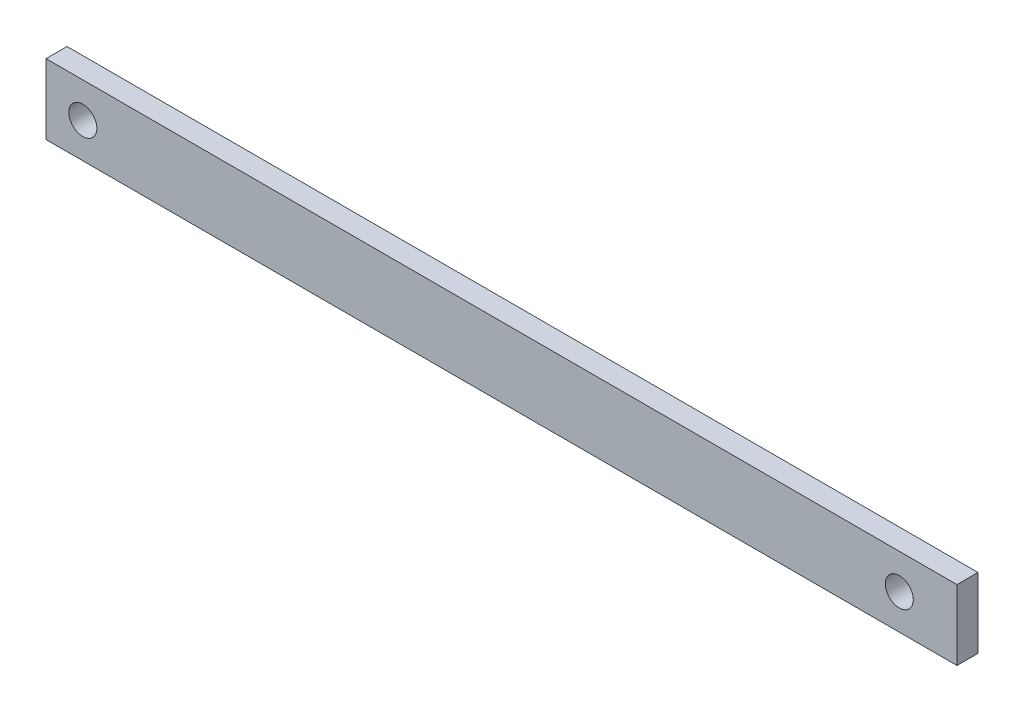
SolidWorks part; units mm, degrees
ref_plane "Front Plane" through (0, 0, 0) normal (0, 0, 1) x (1, 0, 0)
ref_plane "Top Plane" through (0, 0, 0) normal (0, 1, 0) x (1, 0, 0)
ref_plane "Right Plane" through (0, 0, 0) normal (1, 0, 0) x (0, 0, -1)
sketch "Sketch1" plane through (0, 0, 0) normal (0, 0, 1) x (1, 0, 0)
  line L1 (-65, 5) -> (65, 5)
  line L2 (-65, 5) -> (-65, -5)
  line L3 (-65, -5) -> (65, -5)
  line L4 (65, 5) -> (65, -5)
  line L5 (-65, 5) -> (65, -5) construction
  line L6 (-65, -5) -> (65, 5) construction
  point P0 (0, 0)
  dimension "D1" = 130
  dimension "D2" = 10
extrude "Boss-Extrude1" add sketch "Sketch1" along normal blind 3
sketch "Sketch2" plane through (0, 0, 3) normal (0, 0, 1) x (1, 0, 0)
  circle A0 centre (-59.7443, 0) radius 2
  circle A1 centre (56.7676, 0) radius 2
  point P4 (0, 0)
  dimension "D1" = 4
extrude "Cut-Extrude1" cut sketch "Sketch2" against normal blind 10
